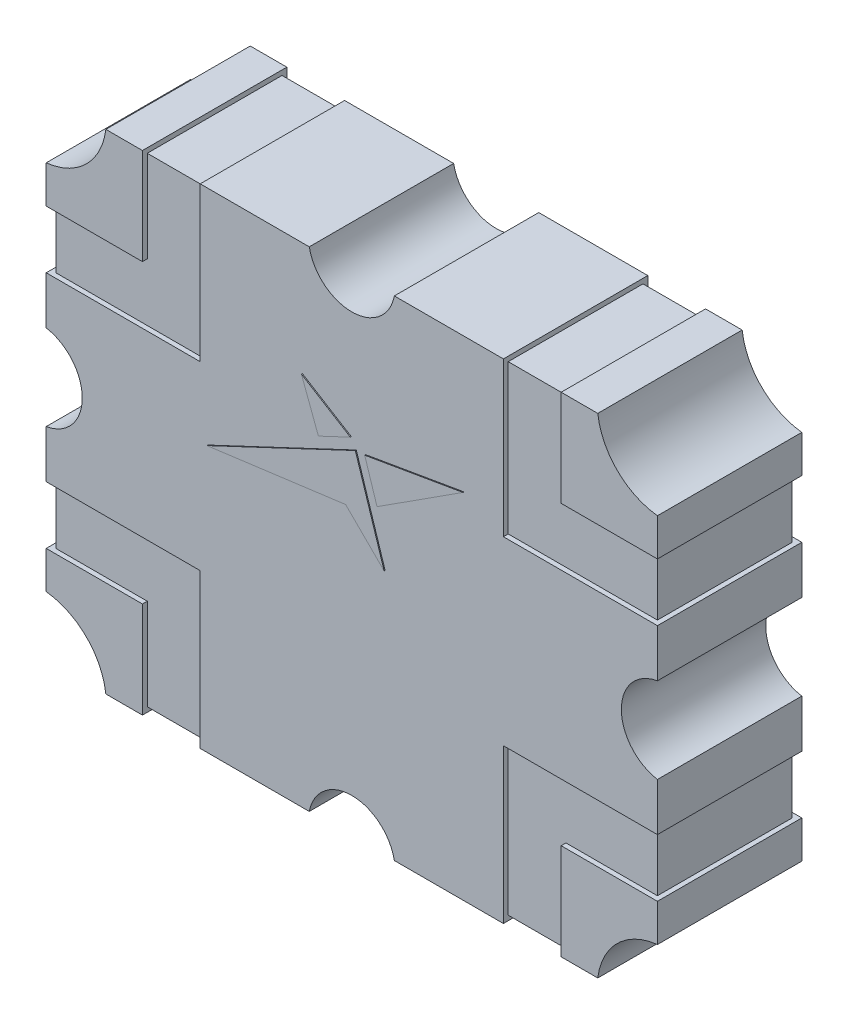
SolidWorks part; units mm, degrees
ref_plane "Front Plane" through (0, 0, 0) normal (0, 0, 1) x (1, 0, 0)
ref_plane "Top Plane" through (0, 0, 0) normal (0, 1, 0) x (1, 0, 0)
ref_plane "Right Plane" through (0, 0, 0) normal (1, 0, 0) x (0, 0, -1)
sketch "Sketch1" plane through (0, 0, 0) normal (0, 0, 1) x (1, 0, 0)
  line L1 (-3.175, 2.54) -> (3.175, 2.54)
  line L2 (-3.175, 2.54) -> (-3.175, -2.54)
  line L3 (-3.175, -2.54) -> (3.175, -2.54)
  line L4 (3.175, 2.54) -> (3.175, -2.54)
  line L5 (-3.175, 2.54) -> (3.175, -2.54) construction
  line L6 (-3.175, -2.54) -> (3.175, 2.54) construction
  point P0 (0, 0)
  dimension "D1" = 6.35
  dimension "D2" = 5.08
extrude "Boss-Extrude1" add sketch "Sketch1" along normal blind 1.5
sketch "Sketch2" plane through (0, 0, 1.5) normal (0, 0, 1) x (1, 0, 0)
  line L1 (-3.25, 2.625) -> (3.25, 2.625) construction
  line L2 (-3.25, 2.625) -> (-3.25, -2.625) construction
  line L3 (-3.25, -2.625) -> (3.25, -2.625) construction
  line L4 (3.25, 2.625) -> (3.25, -2.625) construction
  line L5 (-3.25, 2.625) -> (3.25, -2.625) construction
  line L6 (-3.25, -2.625) -> (3.25, 2.625) construction
  circle A0 centre (-3.25, 2.625) radius 0.7
  circle A1 centre (3.25, 2.625) radius 0.7
  circle A2 centre (3.25, -2.625) radius 0.7
  circle A3 centre (-3.25, -2.625) radius 0.7
  circle A4 centre (0, 2.625) radius 0.45
  circle A5 centre (0, -2.625) radius 0.45
  circle A6 centre (-3.25, 0) radius 0.45
  circle A7 centre (3.25, 0) radius 0.45
  point P0 (0, 0)
  dimension "D3" = 1.4
  dimension "D4" = 0.9
  dimension "D1" = 6.5
  dimension "D2" = 5.25
extrude "Cut-Extrude1" cut sketch "Sketch2" against normal through all
sketch "Sketch3" plane through (0, 0, 1.5) normal (0, 0, 1) x (1, 0, 0)
  line L0 (-3.175, 1.54) -> (-2.175, 1.54)
  line L1 (-3.175, 1.929) -> (-3.175, 0.4437) construction
  line L2 (-2.175, 1.54) -> (-2.175, 2.54)
  line L3 (-0.4419, 2.54) -> (-2.5552, 2.54) construction
  line L4 (-2.175, 2.54) -> (-1.575, 2.54)
  line L5 (-1.575, 2.54) -> (-1.575, 0.94)
  line L6 (-1.575, 0.94) -> (-3.175, 0.94)
  line L7 (-3.175, 0.94) -> (-3.175, 1.54)
  line L8 (0, 0) -> (0, 2.54) construction
  line L9 (0, 0) -> (-3.175, 0) construction
  line L10 (-1.575, -0.94) -> (-3.175, -0.94)
  line L11 (-1.575, -2.54) -> (-1.575, -0.94)
  line L12 (-2.175, -2.54) -> (-1.575, -2.54)
  line L13 (-2.175, -1.54) -> (-2.175, -2.54)
  line L14 (-3.175, -1.54) -> (-2.175, -1.54)
  line L15 (-3.175, -0.94) -> (-3.175, -1.54)
  line L16 (1.575, -2.54) -> (1.575, -0.94)
  line L17 (2.175, -2.54) -> (1.575, -2.54)
  line L18 (2.175, -1.54) -> (2.175, -2.54)
  line L19 (3.175, -1.54) -> (2.175, -1.54)
  line L20 (3.175, -0.94) -> (3.175, -1.54)
  line L21 (1.575, -0.94) -> (3.175, -0.94)
  line L22 (1.575, 0.94) -> (3.175, 0.94)
  line L23 (1.575, 2.54) -> (1.575, 0.94)
  line L24 (2.175, 2.54) -> (1.575, 2.54)
  line L25 (2.175, 1.54) -> (2.175, 2.54)
  line L26 (3.175, 1.54) -> (2.175, 1.54)
  line L27 (3.175, 0.94) -> (3.175, 1.54)
  dimension "D1" = 1
  dimension "D2" = 0.6
extrude "Cut-Extrude2" cut sketch "Sketch3" against normal blind 0.05
sketch "Sketch4" plane through (0, 0, 1.5) normal (0, 0, 1) x (1, 0, 0)
  line L0 (-1.4957, 0.2297) -> (0.0466, 0.956)
  line L1 (0.0466, 0.956) -> (0.3458, 0.023)
  line L2 (0.3458, 0.023) -> (-0.054, 0.4201)
  line L3 (-0.054, 0.4201) -> (-1.4957, 0.2297)
  line L4 (-0.3371, 0.8944) -> (-0.0052, 1.0507)
  line L5 (-0.0052, 1.0507) -> (-0.5138, 1.364)
  line L6 (-0.5138, 1.364) -> (-0.3371, 0.8944)
  line L7 (0.1441, 0.963) -> (0.2721, 0.5639)
  line L8 (0.2721, 0.5639) -> (1.1646, 1.1382)
  line L9 (1.1646, 1.1382) -> (0.1441, 0.963)
  point P9 (-0.035, 0.4528)
  point P11 (0.4383, 0.1916)
  point P12 (-0.035, 0.8907)
  point P13 (-1.4957, 0.2297)
  point P14 (0.5743, 0.1291)
  point P15 (0.7239, -0.1457)
  point P16 (-0.1493, 0.4854)
  point P17 (0.3458, 0.023)
  point P18 (0.0466, 0.956)
  point P19 (-0.054, 0.4201)
  point P20 (-0.5138, 1.364)
  point P21 (1.1347, 1.2063)
  point P22 (0.2642, 0.5589)
  point P23 (1.1646, 1.1382)
extrude "Boss-Extrude2" add sketch "Sketch4" along normal blind 0.01
sketch "Sketch5" plane through (0, 0, 1.45) normal (0, 0, 1) x (1, 0, 0)
  line L0 (-3.175, 0.94) -> (-1.575, 0.94) construction
  line L1 (-3.175, 1.54) -> (-3.125, 1.54)
  line L2 (-3.175, 1.54) -> (-3.175, 0.94)
  line L3 (-3.175, 0.94) -> (-3.125, 0.94)
  line L4 (-3.125, 1.54) -> (-3.125, 0.94)
  line L5 (-1.575, 0.94) -> (-1.575, 2.54) construction
  line L6 (-2.175, 2.54) -> (-1.575, 2.54)
  line L7 (-2.175, 2.54) -> (-2.175, 2.49)
  line L8 (-2.175, 2.49) -> (-1.575, 2.49)
  line L9 (-1.575, 2.54) -> (-1.575, 2.49)
  line L10 (2.175, 1.54) -> (2.175, 2.54) construction
  line L11 (1.575, 2.54) -> (2.175, 2.54)
  line L12 (1.575, 2.54) -> (1.575, 2.49)
  line L13 (1.575, 2.49) -> (2.175, 2.49)
  line L14 (2.175, 2.54) -> (2.175, 2.49)
  line L15 (1.575, 0.94) -> (3.175, 0.94) construction
  line L16 (3.175, 1.54) -> (3.125, 1.54)
  line L17 (3.175, 1.54) -> (3.175, 0.94)
  line L18 (3.175, 0.94) -> (3.125, 0.94)
  line L19 (3.125, 1.54) -> (3.125, 0.94)
  line L20 (2.175, -1.54) -> (3.175, -1.54) construction
  line L21 (3.175, -0.94) -> (3.125, -0.94)
  line L22 (3.175, -0.94) -> (3.175, -1.54)
  line L23 (3.175, -1.54) -> (3.125, -1.54)
  line L24 (3.125, -0.94) -> (3.125, -1.54)
  line L25 (1.575, -0.94) -> (1.575, -2.54) construction
  line L26 (2.175, -2.54) -> (1.575, -2.54)
  line L27 (2.175, -2.54) -> (2.175, -2.49)
  line L28 (2.175, -2.49) -> (1.575, -2.49)
  line L29 (1.575, -2.54) -> (1.575, -2.49)
  line L30 (-2.175, -1.54) -> (-2.175, -2.54) construction
  line L31 (-1.575, -2.54) -> (-2.175, -2.54)
  line L32 (-1.575, -2.54) -> (-1.575, -2.49)
  line L33 (-1.575, -2.49) -> (-2.175, -2.49)
  line L34 (-2.175, -2.54) -> (-2.175, -2.49)
  line L35 (-1.575, -0.94) -> (-3.175, -0.94) construction
  line L36 (-3.175, -1.54) -> (-3.125, -1.54)
  line L37 (-3.175, -1.54) -> (-3.175, -0.94)
  line L38 (-3.175, -0.94) -> (-3.125, -0.94)
  line L39 (-3.125, -1.54) -> (-3.125, -0.94)
  dimension "D1" = 0.05
extrude "Cut-Extrude3" cut sketch "Sketch5" against normal through all
sketch "Sketch6" plane through (0, 0, 0) normal (0, 0, -1) x (-1, 0, 0)
  line L6 (3.175, 1.54) -> (2.175, 1.54)
  line L7 (2.175, 1.54) -> (2.175, 2.54)
  line L8 (2.175, 2.54) -> (1.575, 2.54)
  line L9 (1.575, 2.54) -> (1.575, 0.94)
  line L10 (1.575, 0.94) -> (3.175, 0.94)
  line L11 (3.175, 0.94) -> (3.175, 1.54)
  line L12 (3.175, 1.54) -> (2.175, 1.54)
  line L13 (2.175, 1.54) -> (2.175, 2.54)
  line L14 (2.175, 2.54) -> (1.575, 2.54)
  line L15 (1.575, 2.54) -> (1.575, 0.94)
  line L16 (1.575, 0.94) -> (3.175, 0.94)
  line L17 (3.175, 0.94) -> (3.175, 1.54)
  line L18 (-3.175, 0.94) -> (-1.575, 0.94)
  line L19 (-3.175, 1.54) -> (-3.175, 0.94)
  line L20 (-2.175, 1.54) -> (-3.175, 1.54)
  line L21 (-2.175, 2.54) -> (-2.175, 1.54)
  line L22 (-1.575, 2.54) -> (-2.175, 2.54)
  line L23 (-1.575, 0.94) -> (-1.575, 2.54)
  line L24 (-3.175, 0.94) -> (-1.575, 0.94)
  line L25 (-3.175, 1.54) -> (-3.175, 0.94)
  line L26 (-2.175, 1.54) -> (-3.175, 1.54)
  line L27 (-2.175, 2.54) -> (-2.175, 1.54)
  line L28 (-1.575, 2.54) -> (-2.175, 2.54)
  line L29 (-1.575, 0.94) -> (-1.575, 2.54)
  line L30 (-1.575, -2.54) -> (-1.575, -0.94)
  line L31 (-1.575, -0.94) -> (-3.175, -0.94)
  line L32 (-3.175, -0.94) -> (-3.175, -1.54)
  line L33 (-3.175, -1.54) -> (-2.175, -1.54)
  line L34 (-2.175, -1.54) -> (-2.175, -2.54)
  line L35 (-2.175, -2.54) -> (-1.575, -2.54)
  line L36 (-1.575, -2.54) -> (-1.575, -0.94)
  line L37 (-1.575, -0.94) -> (-3.175, -0.94)
  line L38 (-3.175, -0.94) -> (-3.175, -1.54)
  line L39 (-3.175, -1.54) -> (-2.175, -1.54)
  line L40 (-2.175, -1.54) -> (-2.175, -2.54)
  line L41 (-2.175, -2.54) -> (-1.575, -2.54)
  line L42 (1.575, -2.54) -> (2.175, -2.54)
  line L43 (2.175, -2.54) -> (2.175, -1.54)
  line L44 (2.175, -1.54) -> (3.175, -1.54)
  line L45 (3.175, -1.54) -> (3.175, -0.94)
  line L46 (3.175, -0.94) -> (1.575, -0.94)
  line L47 (1.575, -0.94) -> (1.575, -2.54)
  line L48 (1.575, -2.54) -> (2.175, -2.54)
  line L49 (2.175, -2.54) -> (2.175, -1.54)
  line L50 (2.175, -1.54) -> (3.175, -1.54)
  line L51 (3.175, -1.54) -> (3.175, -0.94)
  line L52 (3.175, -0.94) -> (1.575, -0.94)
  line L53 (1.575, -0.94) -> (1.575, -2.54)
  dimension "D1" = 0
  dimension "D2" = 0
  dimension "D3" = 0
  dimension "D4" = 0
extrude "Cut-Extrude4" cut sketch "Sketch6" against normal blind 0.05
